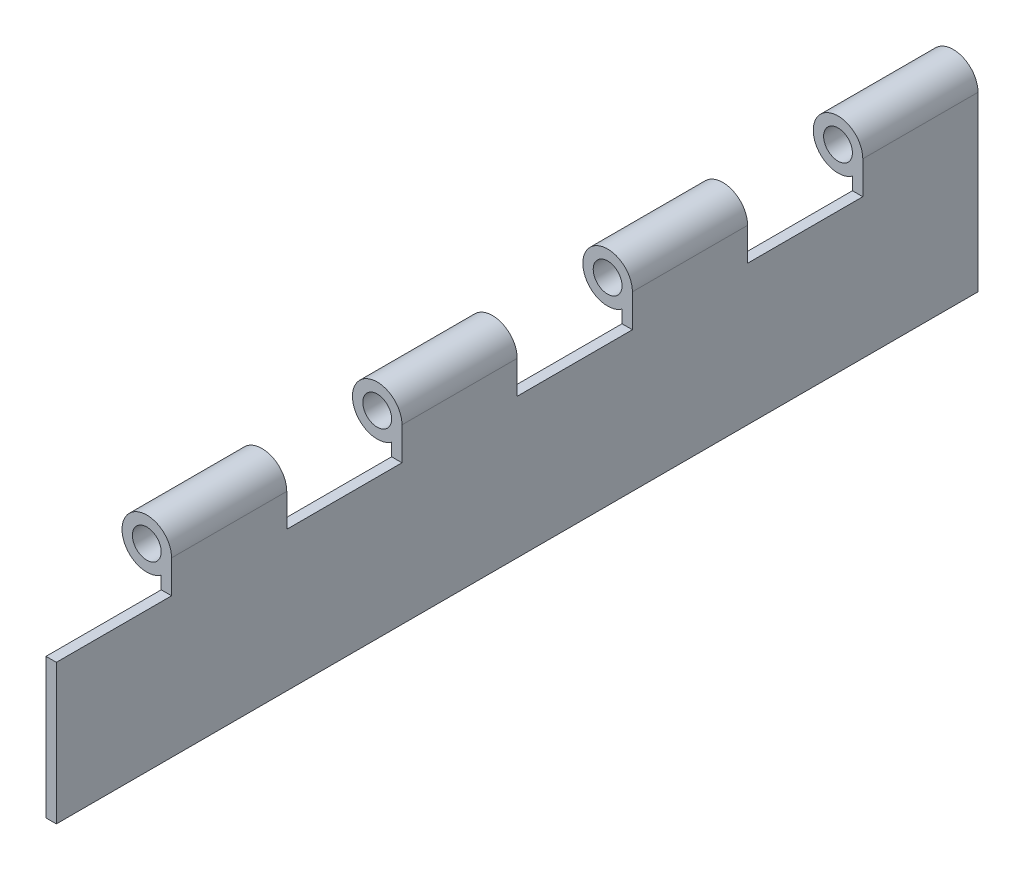
SolidWorks part; units mm, degrees
material "6061 Alloy"
ref_plane "Front Plane" through (0, 0, 0) normal (0, 0, 1) x (1, 0, 0)
ref_plane "Top Plane" through (0, 0, 0) normal (0, 1, 0) x (1, 0, 0)
ref_plane "Right Plane" through (0, 0, 0) normal (1, 0, 0) x (0, 0, -1)
sketch "Sketch1" plane through (0, 0, 0) normal (0, 0, 1) x (1, 0, 0)
  line L0 (5.461, 0) -> (5.461, -38.1)
  line L1 (5.461, -38.1) -> (3.175, -38.1)
  line L2 (3.175, -38.1) -> (3.175, -4.4432)
  circle A0 centre (0, 0) radius 3.175
  arc A1 (5.461, 0) -> (3.175, -4.4432) centre (0, 0) ccw
  circle A2 centre (0, 0) radius 5.461 construction
  dimension "D1" = 6.35
  dimension "D3" = 2.286
  dimension "D4" = 38.1
  dimension "D2" = 2.286
extrude "Boss-Extrude1" add sketch "Sketch1" along normal blind 203.2
sketch "Sketch2" plane through (5.461, 0, 0) normal (1, 0, 0) x (0, 0, -1)
  line L1 (-203.2, 5.461) -> (-177.8, 5.461)
  line L2 (-203.2, 5.461) -> (-203.2, -7.239)
  line L3 (-203.2, -7.239) -> (-177.8, -7.239)
  line L4 (-177.8, 5.461) -> (-177.8, -7.239)
  dimension "D1" = 12.7
  dimension "D2" = 25.4
extrude "Cut-Extrude1" cut sketch "Sketch2" against normal through all
pattern_linear "LPattern1" count 4 spacing 50.8 along (0, 0, -1) of "Cut-Extrude1"
